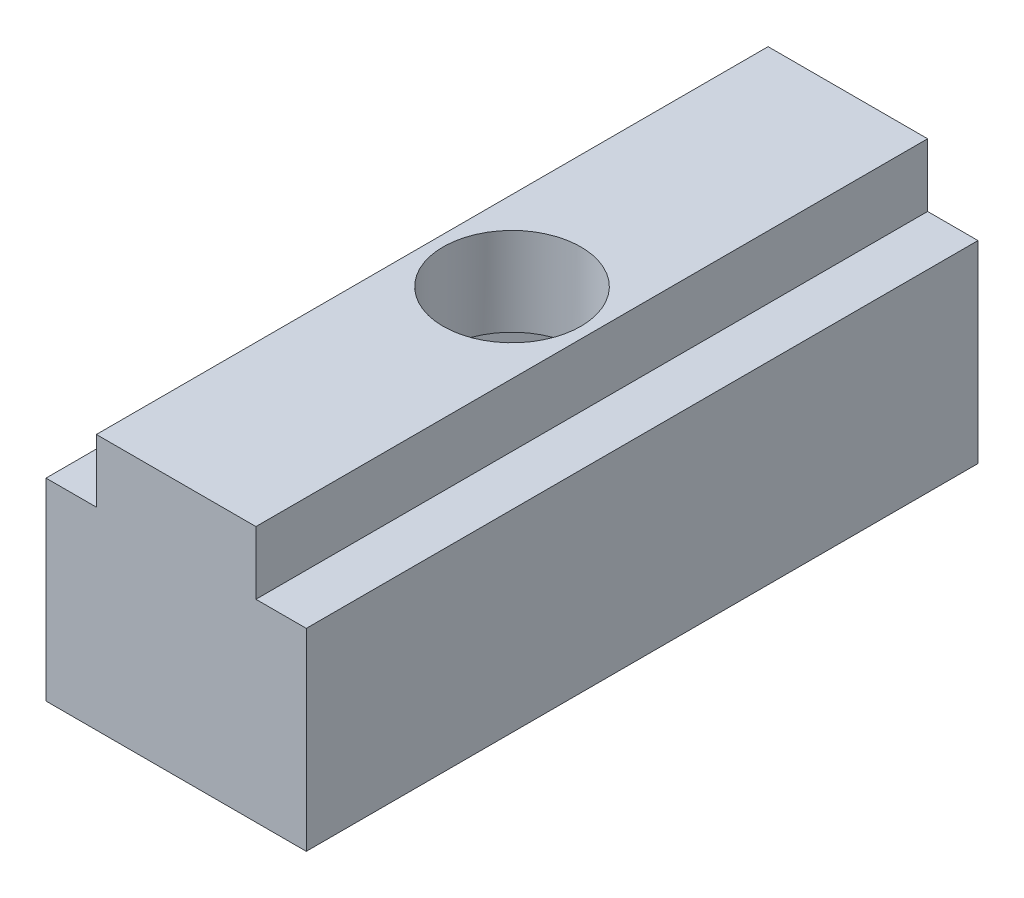
SolidWorks part; units mm, degrees
ref_plane "Front Plane" through (0, 0, 0) normal (1, 0, 0) x (0, 1, 0)
ref_plane "Top Plane" through (0, 0, 0) normal (0, 0, 1) x (0, 1, 0)
ref_plane "Right Plane" through (0, 0, 0) normal (0, 1, 0) x (-1, 0, 0)
sketch "Sketch1" plane through (0, 0, 0) normal (0, 0, 1) x (0, 1, 0)
  line L0 (0, 0) -> (0, 15.5)
  line L1 (0, 15.5) -> (11.5, 15.5)
  line L2 (11.5, 15.5) -> (11.5, 12.5)
  line L3 (11.5, 12.5) -> (15.25, 12.5)
  line L4 (15.25, 12.5) -> (15.25, 3)
  line L5 (15.25, 3) -> (11.5, 3)
  line L6 (11.5, 3) -> (11.5, 0)
  line L7 (11.5, 0) -> (0, 0)
  dimension "D1" = 3.75
  dimension "D2" = 15.5
  dimension "D3" = 9.5
  dimension "D4" = 11.5
extrude "Boss-Extrude1" add sketch "Sketch1" along normal blind 40
sketch "Sketch2" plane through (0, 15.25, 0) normal (0, 1, 0) x (-1, 0, 0)
  line L0 (0, 40) -> (15.5, 0) construction
  circle A0 centre (7.75, 20) radius 4.1
  dimension "D1" = 8.2
extrude "Cut-Extrude1" cut sketch "Sketch2" against normal up to next
sketch "Sketch3" plane through (0, 0, 0) normal (0, -1, 0) x (-1, 0, 0)
  line L1 (2.4408, -14.6947) -> (0.5009, -21.9453)
  line L2 (0.5009, -21.9453) -> (5.8101, -27.2505)
  line L3 (5.8101, -27.2505) -> (13.0592, -25.3053)
  line L4 (13.0592, -25.3053) -> (14.9991, -18.0547)
  line L5 (14.9991, -18.0547) -> (9.6899, -12.7495)
  line L6 (9.6899, -12.7495) -> (2.4408, -14.6947)
  circle A0 centre (7.75, -20) radius 6.5 construction
  dimension "D1" = 13
extrude "Cut-Extrude2" cut sketch "Sketch3" against normal blind 10
